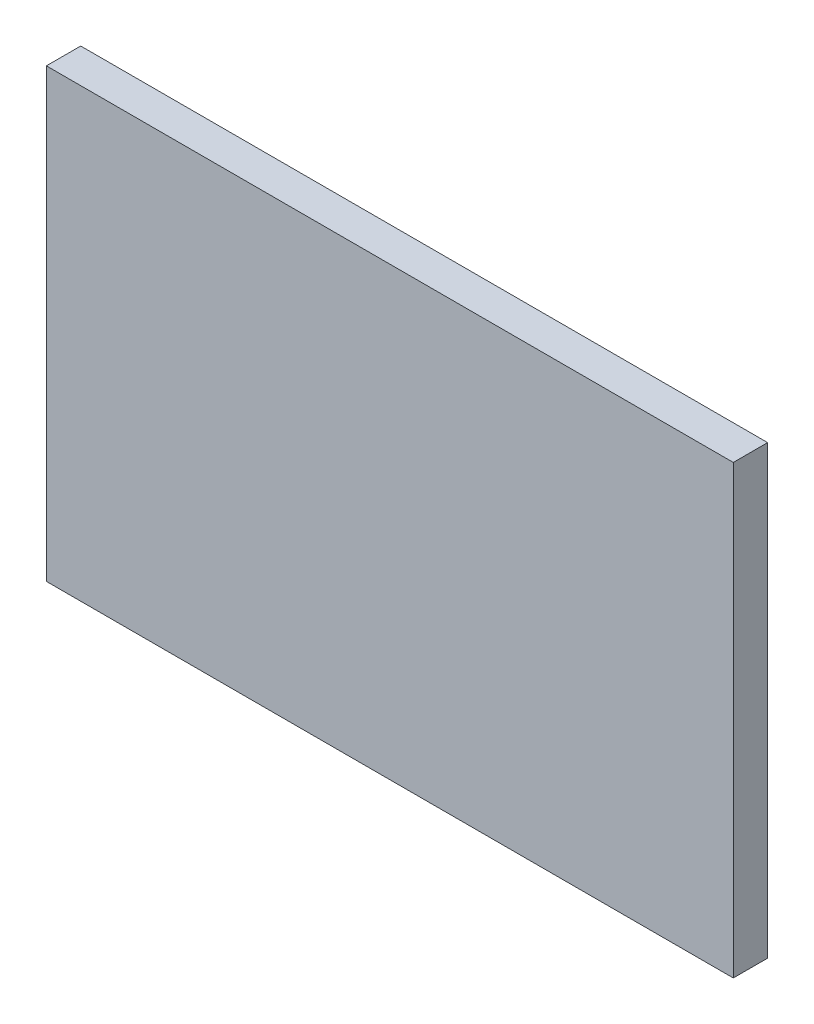
SolidWorks part; units mm, degrees
ref_plane "Front Plane" through (0, 0, 0) normal (0, 0, 1) x (1, 0, 0)
ref_plane "Top Plane" through (0, 0, 0) normal (0, 1, 0) x (1, 0, 0)
ref_plane "Right Plane" through (0, 0, 0) normal (1, 0, 0) x (0, 0, -1)
sketch "Sketch1" plane through (0, 0, 0) normal (0, 0, 1) x (1, 0, 0)
  line L1 (-100, -50) -> (100, -50)
  line L2 (-100, -50) -> (-100, 50)
  line L3 (-100, 50) -> (100, 50)
  line L4 (100, -50) -> (100, 50)
  line L5 (-100, -50) -> (100, 50) construction
  line L6 (-100, 50) -> (100, -50) construction
  point P0 (0, 0)
  dimension "D1" = 200
  dimension "D2" = 100
extrude "Boss-Extrude1" add sketch "Sketch1" along normal blind 10
sketch "Sketch2" plane through (0, 0, 0) normal (0, 0, -1) x (-1, 0, 0)
  line L0 (-6, 0) -> (34, 0) construction
  line L1 (34, 5) -> (-6, 5)
  line L2 (100, 20) -> (100, -20)
  line L3 (34, 5) -> (34, -5)
  line L4 (-6, 5) -> (-6, -5)
  line L5 (34, -5) -> (-6, -5)
  line L8 (90, -20) -> (100, -20)
  line L9 (90, -20) -> (90, 20)
  line L10 (90, 20) -> (100, 20)
  line L11 (-6, -50) -> (-6, 50) construction
  line L12 (90, -20) -> (100, 0) construction
  line L13 (90, 20) -> (100, 0) construction
  line L14 (100, -50) -> (-100, -50) construction
  line L15 (-100, 50) -> (100, 50) construction
  dimension "D1" = 40
  dimension "D2" = 10
  dimension "D3" = 5
  dimension "D4" = 40
  dimension "D5" = 6
extrude "Boss-Extrude2" add sketch "Sketch2" along normal blind 40
sketch "Sketch4" plane through (-100, 0, 0) normal (-1, 0, 0) x (0, 0, 1)
  line L0 (-20, 20) -> (-20, -20) construction
  line L1 (-40, 20) -> (0, 20) construction
  line L2 (-40, -20) -> (0, -20) construction
  circle A0 centre (-20, 0) radius 5
  dimension "D1" = 10
extrude "Cut-Extrude2" cut sketch "Sketch4" against normal blind 31
ref_plane "Plane1" through (-75, 87.7547, -316.8296) normal (0, -0.1034, 0.9946) x (1, 0, 0)
sketch "Sketch7" plane through (0, 0, 0) normal (0, 1, 0) x (1, 0, 0)
  line L4 (100, 0) -> (-100, 0)
  line L5 (100, -10) -> (100, 0)
  line L6 (-100, -10) -> (100, -10)
  line L7 (-100, 0) -> (-100, -10)
  line L8 (100, 0) -> (-100, 0)
  line L9 (100, -10) -> (100, 0)
  line L10 (-100, -10) -> (100, -10)
  line L11 (-100, 0) -> (-100, -10)
  dimension "D1" = 0
extrude "Boss-Extrude3" add sketch "Sketch7" along normal mid plane 130
sketch "Sketch9" plane through (0, 5, 0) normal (0, 1, 0) x (1, 0, 0)
  line L0 (-14, 40) -> (-14, 0) construction
  line L1 (-34, 40) -> (6, 40) construction
  line L2 (-34, 0) -> (6, 0) construction
  circle A0 centre (-14, 20) radius 5
  dimension "D1" = 10
extrude "Cut-Extrude4" cut sketch "Sketch9" against normal blind 130
